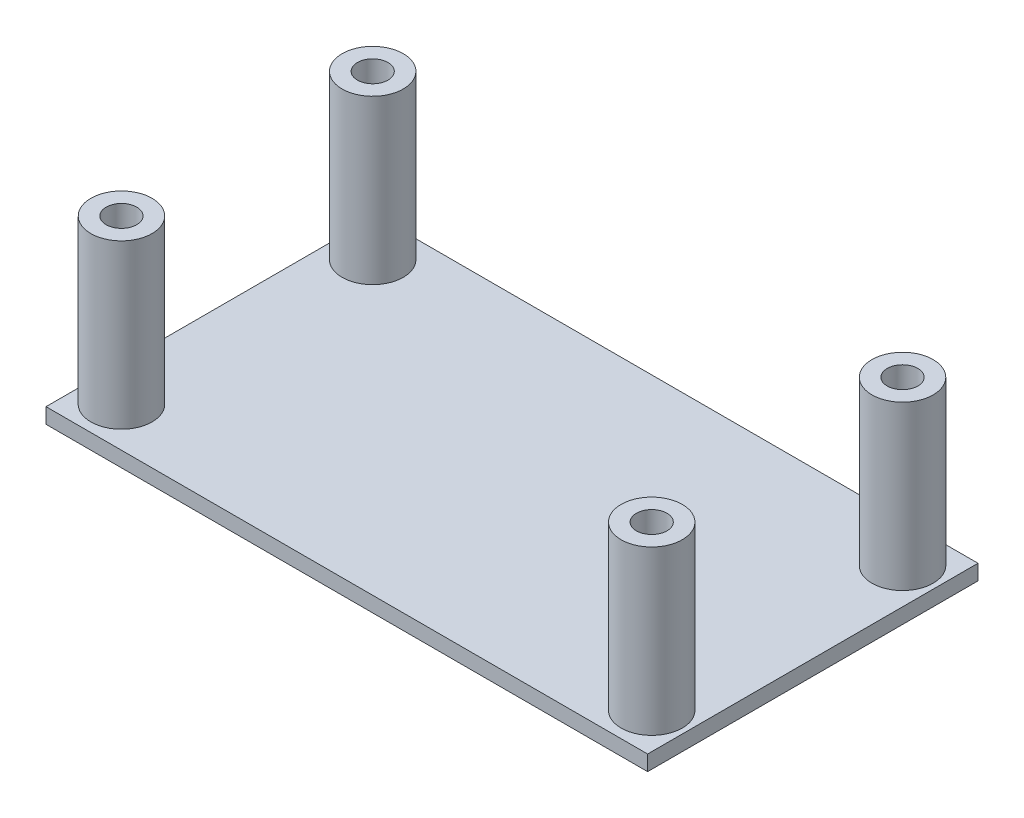
SolidWorks part; units mm, degrees
ref_plane "前视基准面" through (0, 0, 0) normal (0, 0, 1) x (1, 0, 0)
ref_plane "上视基准面" through (0, 0, 0) normal (0, 1, 0) x (1, 0, 0)
ref_plane "右视基准面" through (0, 0, 0) normal (1, 0, 0) x (0, 0, -1)
sketch "草图2" plane through (0, 0, 0) normal (0, 1, 0) x (1, 0, 0)
  line L1 (-24.6381, 15.6657) -> (32.3619, 15.6657)
  line L2 (-24.6381, 15.6657) -> (-24.6381, -24.7343)
  line L3 (-24.6381, -24.7343) -> (32.3619, -24.7343)
  line L4 (32.3619, 15.6657) -> (32.3619, -24.7343)
  dimension "D1" = 57
  dimension "D2" = 40.4
extrude "凸台-拉伸1" add sketch "草图2" along normal blind 1.5
sketch "草图4" plane through (0, 1.5, 0) normal (0, 1, 0) x (1, 0, 0)
  line L0 (-24.6381, 15.6657) -> (-24.6381, -24.7343) construction
  circle A0 centre (-22.0994, 7.7657) radius 1.5
  circle A1 centre (-22.1381, 7.7657) radius 1.5 construction
  circle A2 centre (-22.0994, 7.7657) radius 3
  circle A3 centre (-22.1381, -16.8343) radius 1.5
  circle A4 centre (-22.1381, -16.8343) radius 1.5 construction
  circle A5 centre (-22.1381, -16.8343) radius 3
  circle A9 centre (29.8619, -16.8343) radius 1.5
  circle A10 centre (29.8619, -16.8343) radius 1.5 construction
  circle A11 centre (29.8619, -16.8343) radius 3
  circle A14 centre (29.8619, 7.7657) radius 1.5
  circle A15 centre (29.8619, 7.7657) radius 1.5 construction
  circle A16 centre (29.8619, 7.7657) radius 3
  dimension "D1" = 0
  dimension "D2" = 3
  dimension "D5" = 2.5387
  dimension "D6" = 6
  dimension "D7" = 0
  dimension "D8" = 3
  dimension "D9" = 6
  dimension "D10" = 0
  dimension "D11" = 3
  dimension "D12" = 6
  dimension "D13" = 0
  dimension "D14" = 6
  dimension "D15" = 3
  dimension "D3" = 0
  dimension "D4" = 2.5387
extrude "凸台-拉伸3" add sketch "草图4" along normal blind 16
sketch "草图5" plane through (0, 1.5, 0) normal (0, 1, 0) x (1, 0, 0)
  line L0 (32.3619, 15.6657) -> (-24.6381, 15.6657) construction
  line L1 (-24.6381, 15.6657) -> (32.3619, 15.6657)
  line L2 (-24.6381, 15.6657) -> (-24.6381, 11.6657)
  line L3 (-24.6381, 11.6657) -> (32.3619, 11.6657)
  line L4 (32.3619, 15.6657) -> (32.3619, 11.6657)
  line L5 (-24.6381, 15.6657) -> (-24.6381, 9.3641) construction
  line L6 (32.3619, 9.424) -> (32.3619, 15.6657) construction
  line L7 (32.3619, 10.6657) -> (-24.6381, 10.6657) construction
  line L8 (-24.6381, -18.4926) -> (-24.6381, -24.7343) construction
  line L9 (-24.6381, -20.7343) -> (32.3619, -20.7343)
  line L10 (-24.6381, -20.7343) -> (-24.6381, -24.7343)
  line L11 (-24.6381, -24.7343) -> (32.3619, -24.7343)
  line L12 (32.3619, -20.7343) -> (32.3619, -24.7343)
  line L13 (32.3619, -24.7343) -> (32.3619, -18.4926) construction
  line L14 (-24.6381, -24.7343) -> (32.3619, -24.7343) construction
  line L15 (-24.6381, -19.7343) -> (32.3619, -19.7343) construction
  dimension "D1" = 0
  dimension "D2" = 0
  dimension "D3" = 0
  dimension "D4" = 1
  dimension "D5" = 0
  dimension "D6" = 0
  dimension "D7" = 0
  dimension "D8" = 1
extrude "切除-拉伸1" cut sketch "草图5" against normal through all
sketch "草图6" plane through (0, 1.5, 0) normal (0, 1, 0) x (1, 0, 0)
  line L0 (-24.6381, 11.6657) -> (-24.6381, 9.3641) construction
  line L1 (-25.6381, 11.6657) -> (-24.6381, 11.6657)
  line L2 (-25.6381, 11.6657) -> (-25.6381, -20.7343)
  line L3 (-25.6381, -20.7343) -> (-24.6381, -20.7343)
  line L4 (-24.6381, 11.6657) -> (-24.6381, -20.7343)
  line L5 (-24.6381, 11.6657) -> (32.3619, 11.6657) construction
  line L6 (32.3619, -20.7343) -> (-24.6381, -20.7343) construction
  line L7 (32.3619, -15.176) -> (32.3619, 6.1074) construction
  line L8 (32.3619, 11.6657) -> (33.3619, 11.6657)
  line L9 (32.3619, 11.6657) -> (32.3619, -20.7343)
  line L10 (32.3619, -20.7343) -> (33.3619, -20.7343)
  line L11 (33.3619, 11.6657) -> (33.3619, -20.7343)
  dimension "D1" = 0
  dimension "D2" = 0
  dimension "D3" = 0
  dimension "D4" = 1
  dimension "D5" = 0
  dimension "D6" = 0
  dimension "D7" = 0
  dimension "D8" = 1
extrude "凸台-拉伸4" add sketch "草图6" against normal up to surface (1.5 mm away) up to face at (3.8619, 0, 4.5343)
